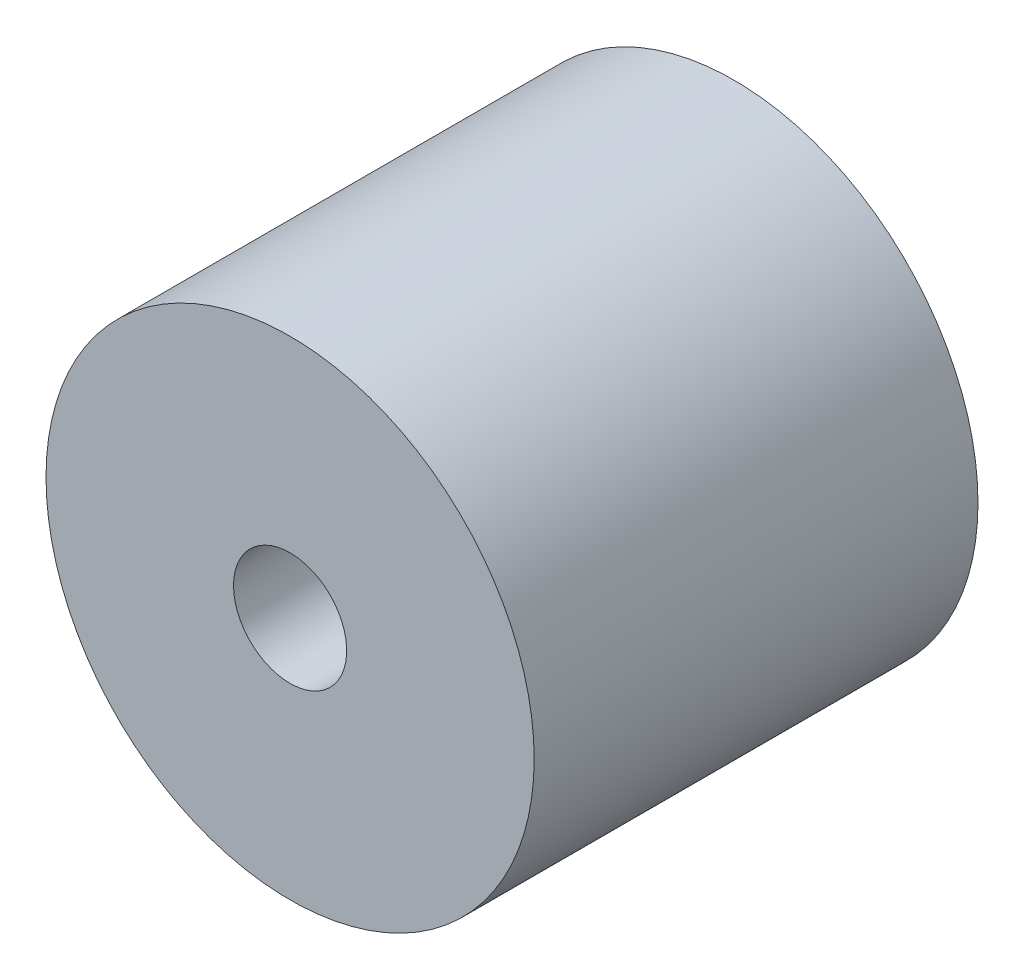
SolidWorks part; units mm, degrees
ref_plane "Front Plane" through (0, 0, 0) normal (0, 0, 1) x (1, 0, 0)
ref_plane "Top Plane" through (0, 0, 0) normal (0, 1, 0) x (1, 0, 0)
ref_plane "Right Plane" through (0, 0, 0) normal (1, 0, 0) x (0, 0, -1)
sketch "Sketch1" plane through (0, 0, 0) normal (0, 0, 1) x (1, 0, 0)
  circle A0 centre (0, 0) radius 11
  dimension "D1" = 22
extrude "Boss-Extrude1" add sketch "Sketch1" along normal blind 20
sketch "Sketch2" plane through (0, 0, 0) normal (0, 0, -1) x (-1, 0, 0)
  circle A0 centre (0, 0) radius 2.55
  point P0 (0, 0)
  dimension "D1" = 5.1
extrude "Cut-Extrude1" cut sketch "Sketch2" against normal blind 20
